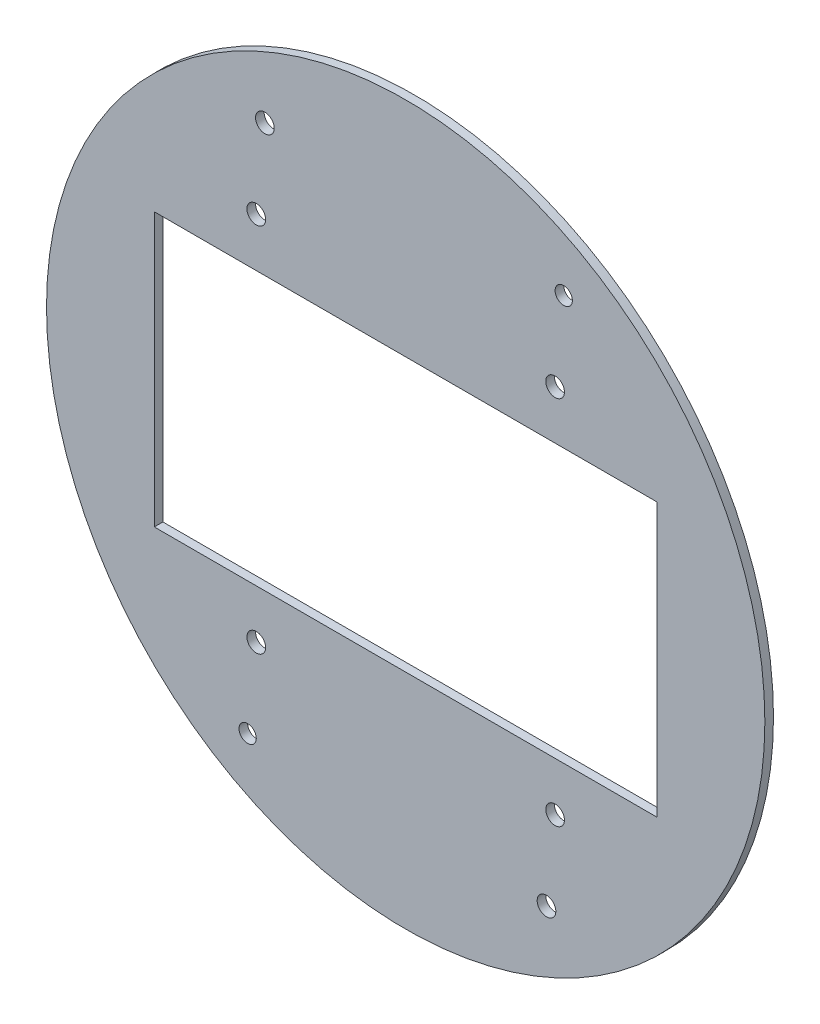
SolidWorks part; units mm, degrees
material "Teak"
ref_plane "Front Plane" through (0, 0, 0) normal (0, 0, 1) x (1, 0, 0)
ref_plane "Top Plane" through (0, 0, 0) normal (0, 1, 0) x (1, 0, 0)
ref_plane "Right Plane" through (0, 0, 0) normal (1, 0, 0) x (0, 0, -1)
sketch "Sketch1" plane through (0, 0, 0) normal (0, 0, 1) x (1, 0, 0)
  line L0 (0, 125) -> (0, -125) construction
  line L1 (-125, 0) -> (125, 0) construction
  line L3 (-87.5, -47.5) -> (87.5, -47.5)
  line L4 (-87.5, -47.5) -> (-87.5, 47.5)
  line L5 (-87.5, 47.5) -> (87.5, 47.5)
  line L6 (87.5, -47.5) -> (87.5, 47.5)
  line L7 (-87.5, -47.5) -> (87.5, 47.5) construction
  line L8 (-87.5, 47.5) -> (87.5, -47.5) construction
  circle A0 centre (0, 0) radius 125
  dimension "D1" = 250
  dimension "D2" = 175
  dimension "D3" = 95
extrude "Boss-Extrude1" add sketch "Sketch1" along normal blind 3
sketch "Sketch2" plane through (0, 0, 3) normal (0, 0, 1) x (1, 0, 0)
  line L0 (0, 125) -> (0, -125) construction
  line L1 (-87.5, -47.5) -> (87.5, -47.5) construction
  line L2 (0, 0) -> (125, 0) construction
  circle A0 centre (0, 0) radius 125 construction
  circle A1 centre (-52, -64.5) radius 3.25
  circle A2 centre (-55, -93.5) radius 3
  circle A3 centre (52, 64.5) radius 3.25
  circle A4 centre (55, 93.5) radius 3
  circle A5 centre (52, -64.5) radius 3.25
  circle A6 centre (-52, 64.5) radius 3.25
  circle A7 centre (49, -93.5) radius 3.25
  circle A8 centre (-49, 93.5) radius 3.25
  point P20 (0, 0)
  point P29 (0, 0)
  dimension "D1" = 6.5
  dimension "D2" = 6
  dimension "D8" = 6.5
  dimension "D11" = 2
  dimension "D3" = 17
  dimension "D4" = 46
  dimension "D5" = 52
  dimension "D6" = 55
  dimension "D7" = 2
  dimension "D9" = 46
  dimension "D10" = 3
  dimension "D12" = 64.5
extrude "Cut-Extrude1" cut sketch "Sketch2" against normal through all
equation "\"D8@Sketch2\"=\"D1@Sketch2\""
equation "\"D9@Sketch2\"=\"D4@Sketch2\""
